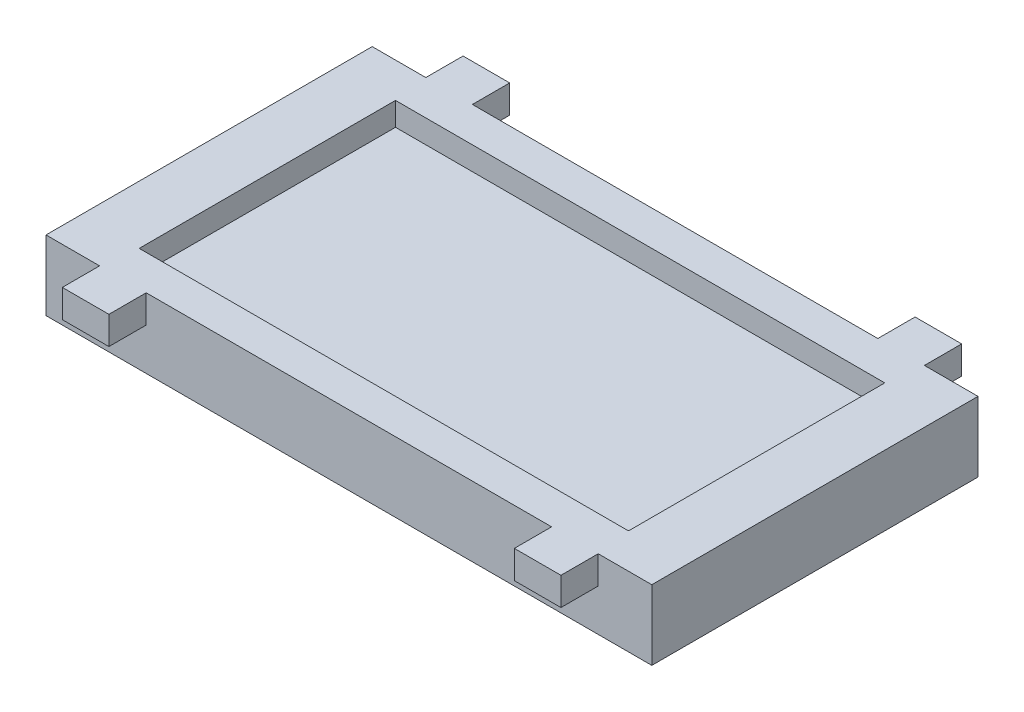
SolidWorks part; units mm, degrees
ref_plane "Front Plane" through (0, 0, 0) normal (0, 0, 1) x (1, 0, 0)
ref_plane "Top Plane" through (0, 0, 0) normal (0, 1, 0) x (1, 0, 0)
ref_plane "Right Plane" through (0, 0, 0) normal (1, 0, 0) x (0, 0, -1)
sketch "Sketch1" plane through (0, 0, 0) normal (0, 1, 0) x (1, 0, 0)
  line L1 (-650, -350) -> (650, -350)
  line L2 (-650, -350) -> (-650, 350)
  line L3 (-650, 350) -> (650, 350)
  line L4 (650, -350) -> (650, 350)
  line L5 (-650, -350) -> (650, 350) construction
  line L6 (-650, 350) -> (650, -350) construction
  point P0 (0, 0)
  dimension "D1" = 1300
  dimension "D2" = 700
extrude "Boss-Extrude1" add sketch "Sketch1" along normal blind 150
sketch "Sketch2" plane through (0, 150, 0) normal (0, 1, 0) x (1, 0, 0)
  line L1 (-525, -275) -> (525, -275)
  line L2 (-525, -275) -> (-525, 275)
  line L3 (-525, 275) -> (525, 275)
  line L4 (525, -275) -> (525, 275)
  line L5 (-525, -275) -> (525, 275) construction
  line L6 (-525, 275) -> (525, -275) construction
  point P0 (0, 0)
  dimension "D1" = 1050
  dimension "D2" = 550
extrude "Cut-Extrude1" cut sketch "Sketch2" against normal blind 50
sketch "Sketch3" plane through (0, 0, 0) normal (0, -1, 0) x (1, 0, 0)
  line L1 (-525, 275) -> (525, 275)
  line L2 (-525, 275) -> (-525, -275)
  line L3 (-525, -275) -> (525, -275)
  line L4 (525, 275) -> (525, -275)
  line L5 (-525, 275) -> (525, -275) construction
  line L6 (-525, -275) -> (525, 275) construction
  point P0 (0, 0)
  dimension "D1" = 550
  dimension "D2" = 1050
extrude "Cut-Extrude2" cut sketch "Sketch3" against normal blind 50
sketch "Sketch14" plane through (0, 150, 0) normal (0, 1, 0) x (1, 0, 0)
  line L0 (535, -350) -> (535, -430)
  line L1 (-650, -350) -> (650, -350) construction
  line L2 (535, -430) -> (435, -430)
  line L3 (435, -430) -> (435, -350)
  line L4 (435, -350) -> (535, -350)
  line L5 (-435, -350) -> (-535, -350)
  line L6 (-535, -350) -> (-535, -430)
  line L7 (-535, -430) -> (-435, -430)
  line L8 (-435, -430) -> (-435, -350)
  line L9 (-650, 350) -> (-650, -350) construction
  line L10 (650, -350) -> (650, 350) construction
  dimension "D1" = 115
  dimension "D2" = 115
  dimension "D3" = 100
  dimension "D4" = 80
  dimension "D5" = 100
  dimension "D6" = 80
extrude "Boss-Extrude3" add sketch "Sketch14" against normal blind 60
sketch "Sketch15" plane through (0, 90, 0) normal (0, -1, 0) x (1, 0, 0)
  line L1 (439.0872, 362.4245) -> (532.0872, 362.4245)
  line L2 (439.0872, 362.4245) -> (439.0872, 417.4245)
  line L3 (439.0872, 417.4245) -> (532.0872, 417.4245)
  line L4 (532.0872, 362.4245) -> (532.0872, 417.4245)
  line L5 (439.0872, 362.4245) -> (532.0872, 417.4245) construction
  line L6 (439.0872, 417.4245) -> (532.0872, 362.4245) construction
  point P0 (485.5872, 389.9245)
  point P5 (487.8092, 391.4628)
  point P6 (485.929, 391.2919)
  point P7 (0, 0)
  dimension "D1" = 93
  dimension "D2" = 55
extrude "Cut-Extrude7" cut sketch "Sketch15" against normal blind 40
sketch "Sketch16" plane through (0, 150, 0) normal (0, 1, 0) x (1, 0, 0)
  line L1 (650, 350) -> (-650, 350) construction
  line L2 (435, 350) -> (535, 350)
  line L3 (535, 430) -> (435, 430)
  line L4 (435, 430) -> (435, 350)
  line L5 (535, 430) -> (535, 350)
  line L6 (-435, 350) -> (-435, 430)
  line L10 (-435, 430) -> (-535, 430)
  line L11 (-535, 430) -> (-535, 350)
  line L12 (-535, 350) -> (-435, 350)
  dimension "D1" = 80
  dimension "D2" = 80
extrude "Boss-Extrude4" add sketch "Sketch16" against normal blind 60
